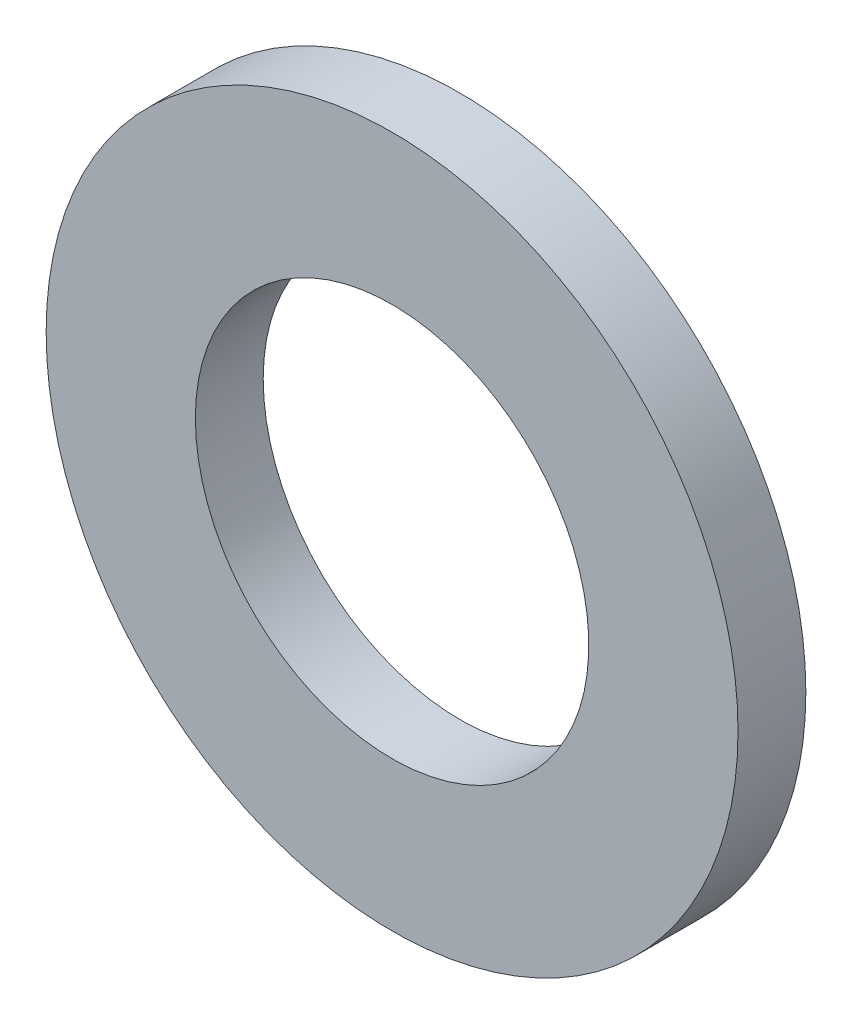
SolidWorks part; units mm, degrees
ref_plane "前视基准面" through (0, 0, 0) normal (0, 0, 1) x (1, 0, 0)
ref_plane "上视基准面" through (0, 0, 0) normal (0, 1, 0) x (1, 0, 0)
ref_plane "右视基准面" through (0, 0, 0) normal (1, 0, 0) x (0, 0, -1)
ref_plane "基准面4" through (0, 0, 0) normal (0, -1, 0) x (1, 0, 0)
sketch "草图1" plane through (0, 0, 0) normal (0, -1, 0) x (1, 0, 0)
  line L0 (1.45, 0.5) -> (1.45, 0)
  line L1 (1.45, 0) -> (2.55, 0)
  line L2 (2.55, 0) -> (2.55, 0.5)
  line L3 (2.55, 0.5) -> (1.45, 0.5)
  line L4 (0, 0.5) -> (0, 0) construction
revolve "旋转1" add sketch "草图1" angle 360 about L4
